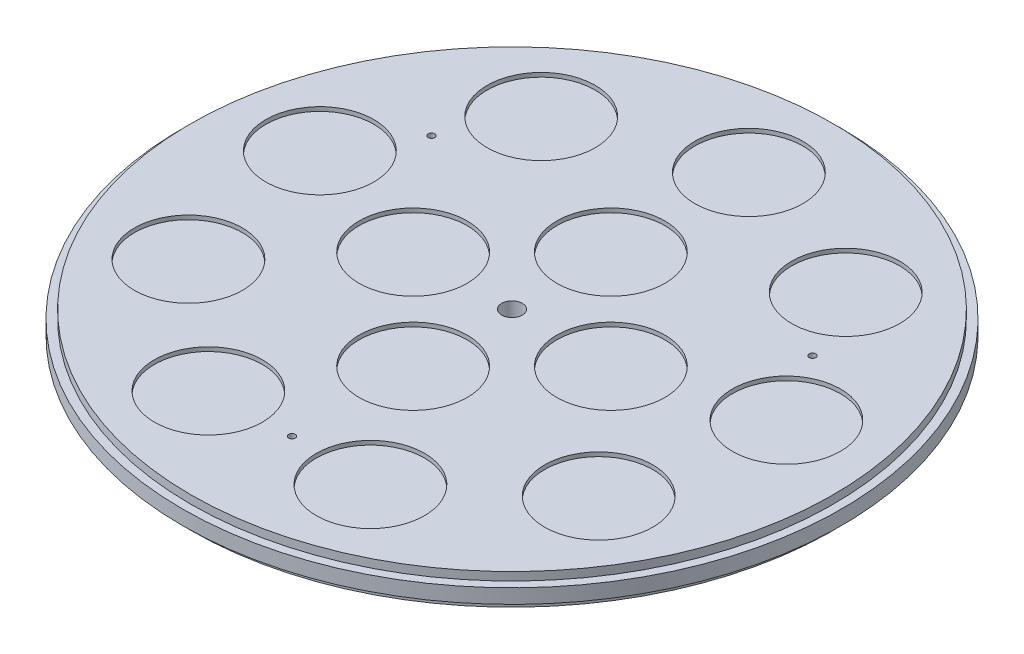
SolidWorks part; units mm, degrees
ref_plane "Plan de face" through (0, 0, 0) normal (0, 0, 1) x (1, 0, 0)
ref_plane "Plan de dessus" through (0, 0, 0) normal (0, 1, 0) x (1, 0, 0)
ref_plane "Plan de droite" through (0, 0, 0) normal (1, 0, 0) x (0, 0, -1)
sketch "Esquisse1" plane through (0, 0, 0) normal (0, 1, 0) x (1, 0, 0)
  circle A0 centre (0, 0) radius 160
  dimension "D1" = 320
extrude "Boss.-Extru.1" add sketch "Esquisse1" along normal mid plane 15
sketch "Esquisse2" plane through (0, -7.5, 0) normal (0, -1, 0) x (1, 0, 0)
  circle A0 centre (0, 0) radius 110.25
  dimension "D1" = 220.5
extrude "Enlèv. mat.-Extru.1" cut sketch "Esquisse2" against normal blind 2
sketch "Esquisse3" plane through (0, -5.5, 0) normal (0, -1, 0) x (-1, 0, 0)
  line L0 (0, 0) -> (0, -110.25) construction
  circle A0 centre (0, 0) radius 110.25 construction
  circle A1 centre (0, -106.8) radius 1.6
  dimension "D1" = 3.2
  dimension "D2" = 106.8
extrude "Enlèv. mat.-Extru.2" cut sketch "Esquisse3" against normal through all
pattern_circular "Répétition circulaire1" count 3 over 360 about axis through (0, 0, 0) along (0, 1, 0) of "Enlèv. mat.-Extru.2"
sketch "Esquisse4" plane through (0, -5.5, 0) normal (0, -1, 0) x (1, 0, 0)
  circle A0 centre (0, 0) radius 1
  dimension "D1" = 2
extrude "Enlèv. mat.-Extru.3" cut sketch "Esquisse4" against normal through all
sketch "Esquisse10" plane through (0, 7.5, 0) normal (0, 1, 0) x (1, 0, 0)
  circle A0 centre (0, 0) radius 5
  dimension "D1" = 10
extrude "Enlèv. mat.-Extru.6" cut sketch "Esquisse10" against normal offset from surface (11 mm away) 2 up to face at (0, -5.5, -1)
sketch "Esquisse11" plane through (0, -7.5, 0) normal (0, 1, 0) x (1, 0, 0)
  circle A0 centre (0, 0) radius 160
  circle A1 centre (0, 0) radius 156
  circle A3 centre (0, 0) radius 160 construction
  dimension "D1" = 4
extrude "Enlèv. mat.-Extru.7" cut sketch "Esquisse11" along normal blind 4
mirror "Symétrie1" about plane through (0, 0, 0) normal (0, 1, 0) of "Enlèv. mat.-Extru.7"
sketch "Esquisse8" plane through (0, 7.5, 0) normal (0, 1, 0) x (1, 0, 0)
  line L0 (0, 115) -> (0, 0) construction
  circle A0 centre (0, 115) radius 26.25
  circle A1 centre (0, 115) radius 33.5 construction
  circle A2 centre (0, 0) radius 152 construction
  circle A3 centre (0, 0) radius 156 construction
  point P20 (0, 0)
  dimension "D1" = 52.5
  dimension "D4" = 4
  dimension "D2" = 67
  dimension "D3" = 115
extrude "Enlèv. mat.-Extru.4" cut sketch "Esquisse8" against normal blind 2
pattern_circular "Répétition circulaire2" count 9 over 360 about axis through (0, 0, 0) along (0, 1, 0) of "Enlèv. mat.-Extru.4"
sketch "Esquisse9" plane through (0, 7.5, 0) normal (0, 1, 0) x (1, 0, 0)
  line L0 (0, 48) -> (0, 0) construction
  circle A0 centre (0, 48) radius 26.25
  circle A1 centre (0, 48) radius 33.5 construction
  dimension "D1" = 52.5
  dimension "D2" = 67
  dimension "D3" = 48
extrude "Enlèv. mat.-Extru.5" cut sketch "Esquisse9" against normal blind 2
pattern_circular "Répétition circulaire3" count 4 over 360 about axis through (0, 0, 0) along (0, 1, 0) of "Enlèv. mat.-Extru.5"
